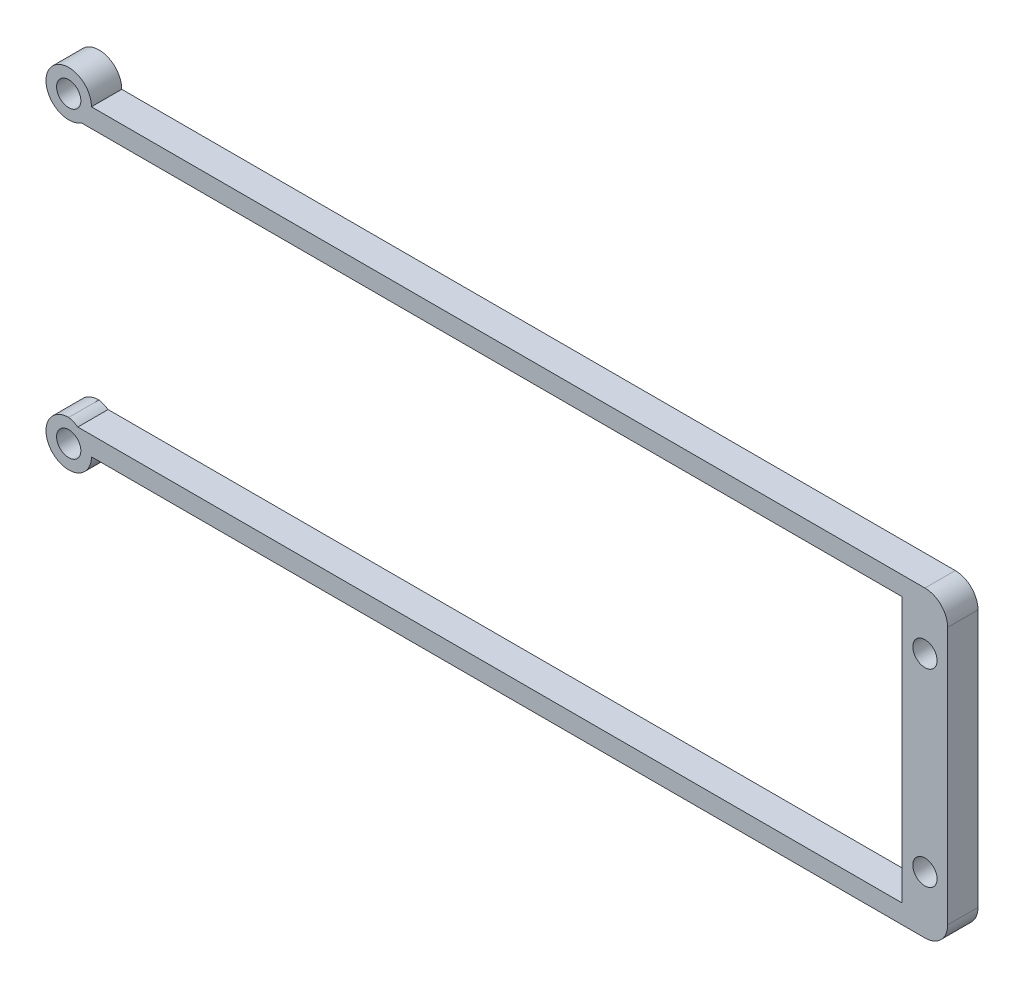
SolidWorks part; units mm, degrees
ref_plane "Front" through (0, 0, 0) normal (0, 0, 1) x (1, 0, 0)
ref_plane "Top" through (0, 0, 0) normal (0, 1, 0) x (1, 0, 0)
ref_plane "Right" through (0, 0, 0) normal (1, 0, 0) x (0, 0, -1)
sketch "Sketch1" plane through (0, 0, 0) normal (0, 0, 1) x (1, 0, 0)
  line L1 (0, 34) -> (106, 34)
  line L2 (0, 34) -> (-3, 34)
  line L4 (0, 0) -> (-3, 0)
  line L6 (0, 0) -> (106, 0)
  line L7 (106, 0) -> (106, 34)
  line L9 (-3, 40) -> (112, 40)
  line L10 (112, 40) -> (112, 0)
  line L11 (-3, -6) -> (112, -6)
  line L12 (112, -6) -> (112, 0)
  arc A0 (-3, 40) -> (-3, 34) centre (-3, 37) ccw
  circle A1 centre (-3, 37) radius 1.6
  arc A2 (-3, 0) -> (-3, -6) centre (-3, -3) ccw
  circle A3 centre (-3, -3) radius 1.6
  circle A4 centre (109, 29.25) radius 1.6
  circle A5 centre (109, 4.75) radius 1.6
extrude "Boss-Extrude1" add sketch "Sketch1" along normal blind 4
sketch "Sketch2" plane through (0, 0, 4) normal (0, 0, 1) x (1, 0, 0)
  line L0 (106, 17) -> (109, 17)
  line L1 (106, 34) -> (106, 0) construction
  circle A0 centre (109, 4.75) radius 1.6
  circle A1 centre (109, 29.25) radius 1.6
extrude "Boss-Extrude2" add sketch "Sketch2" against normal up to surface (4 mm away) up to face at (52.25, 17, 0)
sketch "Sketch3" plane through (0, 0, 4) normal (0, 0, 1) x (1, 0, 0)
  circle A0 centre (109, 29.5) radius 1.6
  circle A1 centre (109, 4.5) radius 1.6
extrude "Cut-Extrude1" cut sketch "Sketch3" against normal blind 4
sketch "Sketch4" plane through (0, 0, 4) normal (0, 0, 1) x (1, 0, 0)
  line L0 (112, 40) -> (113, 40)
  line L1 (112, 40) -> (112, -6)
  line L2 (112, -6) -> (113, -6)
  line L3 (113, -6) -> (113, 40)
  line L4 (109, 29.5) -> (110, 29.5)
  circle A0 centre (110, 29.5) radius 1.6
  circle A1 centre (110, 4.5437) radius 1.6
  circle A3 centre (109, 29.5) radius 1.6
  circle A4 centre (109, 4.5) radius 1.6
  circle M3 centre (109, 29.5) radius 1.6
  circle M4 centre (109, 4.5) radius 1.6
  circle M5 centre (-3, 37) radius 1.6
  line M6 (106, 0) -> (-3, 0)
  arc M7 (-3, 0) -> (-3, -6) centre (-3, -3) ccw
  line M8 (-3, -6) -> (112, -6)
  line M9 (112, -6) -> (112, 40)
  line M10 (112, 40) -> (-3, 40)
  arc M11 (-3, 40) -> (-3, 34) centre (-3, 37) ccw
  line M12 (-3, 34) -> (106, 34)
  line M13 (106, 34) -> (106, 0)
  circle M14 centre (-3, -3) radius 1.6
extrude "Boss-Extrude4" add sketch "Sketch4" against normal up to surface (4 mm away) contours A1 M4 | L2 L3 L0 M9 | A0 M3 | A1 A0 M13 M6 M7 M8 M9 M10 M11 M12 M4 M3 M14 M5
sketch "Sketch6" plane through (0, 0, 4) normal (0, 0, 1) x (1, 0, 0)
  line L0 (106, 34) -> (106, 0)
  line L1 (106, 0) -> (107, 0)
  line L2 (107, 0) -> (107, 34)
  line L3 (107, 34) -> (106, 34)
  circle A0 centre (110, 4.5437) radius 1.6
  circle A1 centre (110, 29.5) radius 1.6
extrude "Cut-Extrude2" cut sketch "Sketch6" against normal blind 4
sketch "Sketch7" plane through (0, 0, 4) normal (0, 0, 1) x (1, 0, 0)
  line L0 (52, 0) -> (-3, 0)
  line L1 (-3, 34) -> (107, 34) construction
  line L2 (52, 34.5) -> (-1.3417, 34.5)
  line L3 (107, 34) -> (107, 34.5)
  line L5 (52, 34.5) -> (107, 34.5)
  line L6 (52, 34) -> (107, 34)
  line L7 (52, 34) -> (-3, 34)
  line L9 (52, 0) -> (107, 0)
  line L10 (52, -0.5) -> (107, -0.5)
  line L11 (107, 0) -> (107, -0.5)
  line L12 (52, -0.5) -> (-1.801, -0.5)
  arc A0 (-3, 34) -> (-1.3417, 34.5) centre (-3, 37) ccw
  arc A1 (-3, 0) -> (-1.801, -0.5) centre (-3.5278, -2.9532) cw
extrude "Cut-Extrude4" cut sketch "Sketch7" against normal blind 4
fillet "Fillet2" radius 3 2 edges at (113, 40, 2) (113, -6, 2)
sketch "Sketch8" plane through (0, 0, 4) normal (0, 0, 1) x (1, 0, 0)
  line L0 (0, 37) -> (113, 37)
  line L1 (113, 37) -> (119.401, 46.5513)
  line L2 (119.401, 46.5513) -> (-5.4709, 48.6399)
  line L3 (-5.4709, 48.6399) -> (-3, 40)
  line L4 (0, -3) -> (113, -3)
  line L5 (113, -3) -> (122.3848, -22.5236)
  line L6 (122.3848, -22.5236) -> (1.0935, -19.3906)
  line L7 (1.0935, -19.3906) -> (-3, -6)
  arc A0 (0, 37) -> (-3, 40) centre (-3, 37) ccw
  arc A1 (-3, -6) -> (0, -3) centre (-3, -3) ccw
extrude "Cut-Extrude5" cut sketch "Sketch8" against normal blind 10
fillet "Fillet3" radius 3 2 edges at (113, -3, 2) (113, 37, 2)
